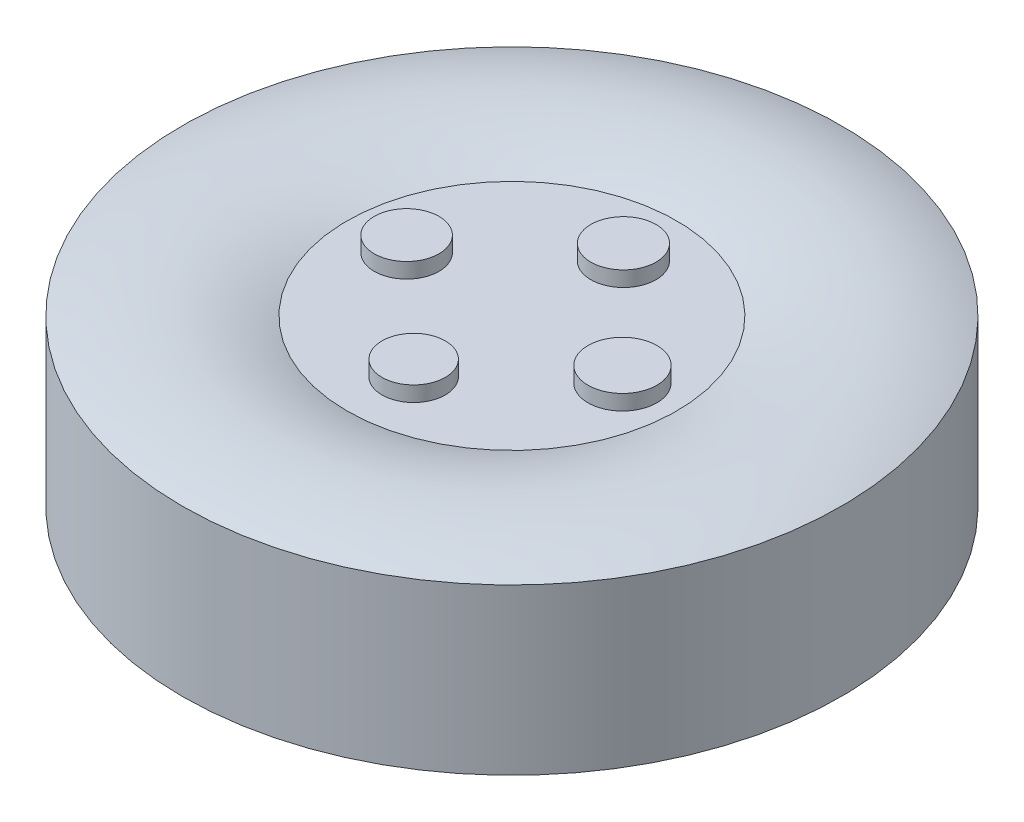
SolidWorks part; units mm, degrees
ref_plane "Front Plane" through (0, 0, 0) normal (0, 0, 1) x (1, 0, 0)
ref_plane "Top Plane" through (0, 0, 0) normal (0, 1, 0) x (1, 0, 0)
ref_plane "Right Plane" through (0, 0, 0) normal (1, 0, 0) x (0, 0, -1)
sketch "Sketch4" plane through (0, 0, 0) normal (0, 0, 1) x (1, 0, 0)
  line L5 (-77.8627, 20.3872) -> (-77.3627, 20.3872)
  line L10 (-77.8627, 20.3872) -> (-77.8627, 19.8872)
  line L11 (-77.8627, 19.8872) -> (-77.3627, 19.8872)
  line L12 (-76.8627, 20.3872) -> (-76.8627, 19.8872)
  arc A1 (-77.3627, 20.3872) -> (-76.8627, 20.3872) centre (-77.1127, 19.7354) cw
  arc A2 (-77.3627, 19.8872) -> (-76.8627, 19.8872) centre (-77.1127, 20.5411) ccw
  dimension "D2" = 0.5
  dimension "D3" = 0.7
  dimension "D1" = 1
revolve "Revolve1" add sketch "Sketch4" angle 360 about L10
sketch "Sketch5" plane through (0, 20.3872, 0) normal (0, 1, 0) x (1, 0, 0)
  line L0 (-79.0192, 0.0249) -> (-76.0184, -0.0419) construction
  line L1 (-76.0184, -0.0419) -> (-77.8208, 1.0862) construction
  line L2 (-77.8208, 1.0862) -> (-77.8709, -1.1626) construction
  line L3 (-77.8709, -1.1626) -> (-76.8343, -0.9435) construction
  line L4 (-76.8343, -0.9435) -> (-76.1724, -0.6631) construction
  circle A0 centre (-77.838, 0.3137) radius 0.099
  circle A1 centre (-77.5188, -0.0085) radius 0.1045
  circle A2 centre (-77.8519, -0.3088) radius 0.096
  circle A3 centre (-78.1885, 0.0064) radius 0.0983
  point P12 (0, 0)
  point P15 (-78.1885, 0)
extrude "Boss-Extrude2" add sketch "Sketch5" along normal through all and the other way through all
